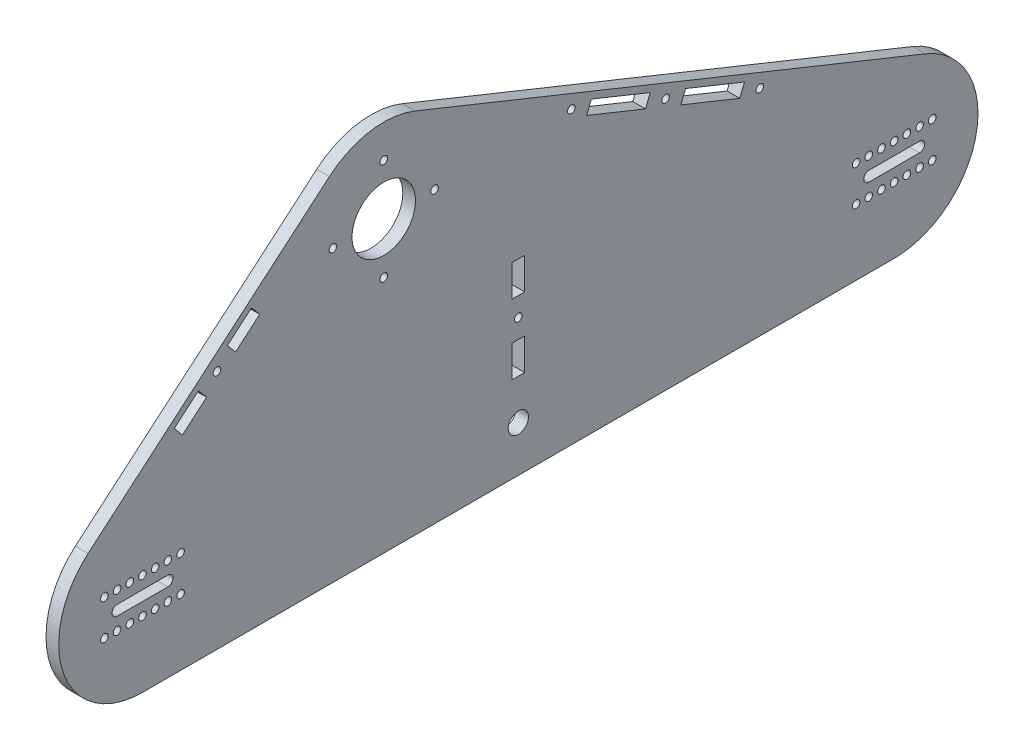
SolidWorks part; units mm, degrees
material "PMMA"
ref_plane "Piano frontale" through (0, 0, 0) normal (0, 0, 1) x (1, 0, 0)
ref_plane "Piano superiore" through (0, 0, 0) normal (0, 1, 0) x (1, 0, 0)
ref_plane "Piano destro" through (0, 0, 0) normal (1, 0, 0) x (0, 0, -1)
sketch "Schizzo5" plane through (0, 0, 0) normal (1, 0, 0) x (0, 0, -1)
  line L0 (-95, 0) -> (201, 0) construction
  line L1 (0, 81) -> (0, 0) construction
  dimension "D1" = 95
  dimension "D2" = 201
  dimension "D3" = 81
sketch "Schizzo2" plane through (0, 0, 0) normal (1, 0, 0) x (0, 0, -1)
  line L0 (20, 81) -> (-20, 81) construction
  line L1 (0, 101) -> (0, 61) construction
  circle A0 centre (-95, 0) radius 2
  circle A1 centre (201, 0) radius 2
  circle A2 centre (0, 81) radius 12.5
  circle A3 centre (0, 101) radius 1.5
  circle A4 centre (20, 81) radius 1.5
  circle A5 centre (-20, 81) radius 1.5
  circle A6 centre (0, 61) radius 1.5
  point P15 (0, 81)
  point P16 (0, 81)
  dimension "D1" = 4
  dimension "D2" = 25
  dimension "D3" = 3
  dimension "D4" = 40
  dimension "D5" = 40
sketch "Schizzo3" plane through (0, 0, 0) normal (1, 0, 0) x (0, 0, -1)
  line L0 (-95, 0) -> (-95, -14.8819) construction
  line L1 (201, 0) -> (201, -14.8819) construction
  line L2 (-95, -33) -> (201, -33)
  line L3 (-116.4107, 25.1114) -> (-21.4107, 106.1114)
  line L4 (12.3346, 111.6081) -> (213.3346, 30.6081)
  line L5 (-90.8456, 91.3374) -> (-46.9759, 39.8853) construction
  line L6 (125.4712, 102.4655) -> (100.1981, 39.7507) construction
  line L7 (53, 29.8908) -> (53, -95.8908) construction
  line L9 (184.7962, 36.718) -> (37.1353, 96.2231) construction
  arc A0 (12.3346, 111.6081) -> (-21.4107, 106.1114) centre (0, 81) ccw
  arc A1 (-116.4107, 25.1114) -> (-95, -33) centre (-95, 0) ccw
  arc A2 (213.3346, 30.6081) -> (201, -33) centre (201, 0) cw
  circle A3 centre (-95, 0) radius 47.625 construction
  circle A4 centre (201, 0) radius 47.625 construction
  circle A11 centre (-65.6667, 61.8066) radius 1.5
  circle A12 centre (110.9657, 66.4705) radius 1.5
  circle A13 centre (73.865, 81.4216) radius 1.5
  circle A14 centre (148.0665, 51.5195) radius 1.5
  point P19 (-68.9107, 65.6114)
  point P22 (112.8346, 71.1081)
  point P32 (53, -33)
  point P44 (110.9657, 66.4705)
  dimension "D2" = 33
  dimension "D3" = 95.25
  dimension "D11" = 5
  dimension "D12" = 40
  dimension "D13" = 40
  dimension "D20" = 5
extrude "Estrusione-Estrusione1" add sketch "Schizzo3" along normal blind 5
extrude "Taglio-Estrusione1" cut sketch "Schizzo2" along normal through all
sketch "Schizzo4" plane through (0, 0, 0) normal (1, 0, 0) x (0, 0, -1)
  line L5 (53, -2.6867) -> (53, -128.4682) construction
  line L11 (53, 29.8908) -> (53, -95.8908) construction
  line L24 (73.865, 81.4216) -> (110.9657, 66.4705) construction
  line L29 (80.8214, 78.6183) -> (104.0093, 69.2739) construction
  line L30 (104.9438, 71.5926) -> (103.0749, 66.9551)
  line L31 (103.0749, 66.9551) -> (79.8869, 76.2995)
  line L32 (81.7558, 80.9371) -> (79.8869, 76.2995)
  line L33 (104.9438, 71.5926) -> (81.7558, 80.9371)
  line L34 (100.1981, 39.7507) -> (119.4142, 87.4352) construction
  line L35 (125.4712, 102.4655) -> (100.1981, 39.7507) construction
  line L36 (118.8566, 65.986) -> (116.9877, 61.3484)
  line L37 (116.9877, 61.3484) -> (140.1757, 52.004)
  line L38 (142.0445, 56.6416) -> (140.1757, 52.004)
  line L39 (118.8566, 65.986) -> (142.0445, 56.6416)
  line L40 (-82.5077, 50.7328) -> (-72.9958, 58.8429)
  line L41 (-72.9958, 58.8429) -> (-69.7518, 55.0382)
  line L42 (-69.7518, 55.0382) -> (-79.2637, 46.928)
  line L43 (-79.2637, 46.928) -> (-82.5077, 50.7328)
  line L44 (-46.9759, 39.8853) -> (-90.8456, 91.3374) construction
  line L45 (-116.4107, 25.1114) -> (-21.4107, 106.1114) construction
  line L46 (-80.8857, 48.8304) -> (-50.4477, 74.7828) construction
  line L47 (-61.5816, 68.5751) -> (-58.3375, 64.7703)
  line L48 (-52.0697, 76.6852) -> (-61.5816, 68.5751)
  line L49 (-48.8257, 72.8804) -> (-52.0697, 76.6852)
  line L50 (-58.3375, 64.7703) -> (-48.8257, 72.8804)
  point P51 (92.4154, 73.9461)
  point P64 (-80.8857, 48.8304)
  point P71 (-65.6667, 61.8066)
  dimension "D14" = 25
  dimension "D15" = 5
  dimension "D16" = 12.5
  dimension "D17" = 5
  dimension "D18" = 40
extrude "Taglio-Estrusione2" cut sketch "Schizzo4" along normal through all
sketch "Schizzo6" plane through (0, 0, 0) normal (1, 0, 0) x (0, 0, -1)
  line L0 (-105, 0) -> (-85, 0) construction
  line L1 (-105, 2) -> (-85, 2)
  line L2 (-105, -2) -> (-85, -2)
  line L3 (191, 0) -> (211, 0) construction
  line L4 (191, 2) -> (211, 2)
  line L5 (191, -2) -> (211, -2)
  line L6 (-95.8595, 7) -> (49904.1405, 7) construction
  line L7 (-107.9229, 6.9974) -> (49892.0771, 6.9974) construction
  line L8 (-95, 0) -> (-95, 7) construction
  line L9 (-56.257, -7) -> (-50056.257, -7) construction
  line L10 (53, -29.7252) -> (53, 29.7252) construction
  line L11 (-95, 0) -> (201, 0) construction
  line L12 (-95, -33) -> (201, -33) construction
  line L13 (6.9793, 20.84) -> (99.0207, 20.84) construction
  line L14 (50.5, 40.84) -> (55.5, 40.84)
  line L15 (50.5, 40.84) -> (50.5, 28.34)
  line L16 (50.5, 28.34) -> (55.5, 28.34)
  line L17 (55.5, 40.84) -> (55.5, 28.34)
  line L18 (50.5, 0.84) -> (55.5, 0.84)
  line L19 (50.5, 0.84) -> (50.5, 13.34)
  line L20 (50.5, 13.34) -> (55.5, 13.34)
  line L21 (55.5, 0.84) -> (55.5, 13.34)
  line L22 (53, 28.34) -> (53, 13.34) construction
  line L23 (53, 29.8908) -> (53, -95.8908) construction
  arc A0 (-105, 2) -> (-105, -2) centre (-105, 0) ccw
  arc A1 (-85, -2) -> (-85, 2) centre (-85, 0) ccw
  arc A2 (191, 2) -> (191, -2) centre (191, 0) ccw
  arc A3 (211, -2) -> (211, 2) centre (211, 0) ccw
  circle A4 centre (-95, 7) radius 1.5
  circle A5 centre (-90, 7) radius 1.5
  circle A6 centre (-85, 7) radius 1.5
  circle A7 centre (-80, 7) radius 1.5
  circle A8 centre (53, -15) radius 4
  circle A9 centre (53, 20.84) radius 1.5
  circle A10 centre (-100, 7) radius 1.5
  circle A11 centre (-105, 7) radius 1.5
  circle A12 centre (-110, 7) radius 1.5
  circle A17 centre (-80, -7) radius 1.5
  circle A18 centre (-85, -7) radius 1.5
  circle A19 centre (-90, -7) radius 1.5
  circle A20 centre (-95, -7) radius 1.5
  circle A21 centre (-100, -7) radius 1.5
  circle A22 centre (-105, -7) radius 1.5
  circle A23 centre (-110, -7) radius 1.5
  circle A28 centre (216, -7) radius 1.5
  circle A29 centre (211, -7) radius 1.5
  circle A30 centre (206, -7) radius 1.5
  circle A31 centre (201, -7) radius 1.5
  circle A32 centre (196, -7) radius 1.5
  circle A33 centre (191, -7) radius 1.5
  circle A34 centre (186, -7) radius 1.5
  circle A39 centre (186, 7) radius 1.5
  circle A40 centre (191, 7) radius 1.5
  circle A41 centre (196, 7) radius 1.5
  circle A42 centre (201, 7) radius 1.5
  circle A43 centre (206, 7) radius 1.5
  circle A44 centre (211, 7) radius 1.5
  circle A45 centre (216, 7) radius 1.5
  point P2 (-95, 0)
  point P11 (201, 0)
  point P30 (53, 0)
  point P31 (53, 0)
  point P54 (53, 20.84)
  dimension "D2" = 2
  dimension "D4" = 2
  dimension "D7" = 3
  dimension "D10" = 8
  dimension "D13" = 3
  dimension "D1" = 10
  dimension "D3" = 10
  dimension "D5" = 7
  dimension "D6" = 7
  dimension "D11" = 18
  dimension "D12" = 5
  dimension "D14" = 12.5
  dimension "D15" = 40
  dimension "D16" = 35.84
  dimension "D8" = 4
  dimension "D9" = 4
extrude "Taglio-Estrusione4" cut sketch "Schizzo6" along direction (1, 0, 0) on the side of the normal through all
sketch "Schizzo8" plane through (0, 0, 0) normal (1, 0, 0) x (0, 0, -1)
  line L0 (0, 84) -> (0, 93.5) construction
  line L1 (-0.5, 84.958) -> (-0.5, 83.958)
  line L2 (0.5, 84.958) -> (0.5, 83.958)
  line L3 (3.958, 80.5) -> (2.958, 80.5)
  line L4 (3.958, 81.5) -> (2.958, 81.5)
  line L5 (-0.5, 77.042) -> (-0.5, 78.042)
  line L6 (0.5, 77.042) -> (0.5, 78.042)
  line L7 (-3.958, 81.5) -> (-2.958, 81.5)
  line L8 (-3.958, 80.5) -> (-2.958, 80.5)
  circle A0 centre (0, 81) radius 2
  circle A1 centre (0, 81) radius 3
  circle A2 centre (0, 81) radius 12.5 construction
  arc A3 (-0.5, 84.958) -> (0.5, 84.958) centre (0, 83.2038) cw
  arc A4 (-0.5, 83.958) -> (0.5, 83.958) centre (0, 81) cw
  arc A5 (2.958, 81.5) -> (2.958, 80.5) centre (0, 81) cw
  arc A6 (3.958, 81.5) -> (3.958, 80.5) centre (2.2038, 81) cw
  arc A7 (0.5, 78.042) -> (-0.5, 78.042) centre (0, 81) cw
  arc A8 (0.5, 77.042) -> (-0.5, 77.042) centre (0, 78.7962) cw
  arc A9 (-2.958, 80.5) -> (-2.958, 81.5) centre (0, 81) cw
  arc A10 (-3.958, 80.5) -> (-3.958, 81.5) centre (-2.2038, 81) cw
  point P33 (0, 81)
  dimension "D1" = 4
  dimension "D2" = 6
  dimension "D5" = 4
  dimension "D3" = 0.5
  dimension "D4" = 0.5
  dimension "D6" = 1
  dimension "D7" = 1
extrude "Estrusione-Estrusione2" [suppressed] add sketch "Schizzo8" along normal blind 5 contours A1 A4 A0 | L0 A1 L2 A3 | A4 L0 A3 L1 | A10 L8 A1 L7 | A8 L6 A1 L5 | A6 L4 A1 L3
equation "\"Thickness\"=5"
equation "\"D1@Estrusione-Estrusione1\"=\"Thickness\""
equation "\"D17@Schizzo4\"=\"Thickness\""
equation "\"D15@Schizzo4\"=\"Thickness\""
equation "\"D6@Schizzo6\"=\"D5@Schizzo6\""
equation "\"D1@Estrusione-Estrusione2\"=\"Thickness\""
equation "\"D5@Schizzo2\"=\"D4@Schizzo2\""
